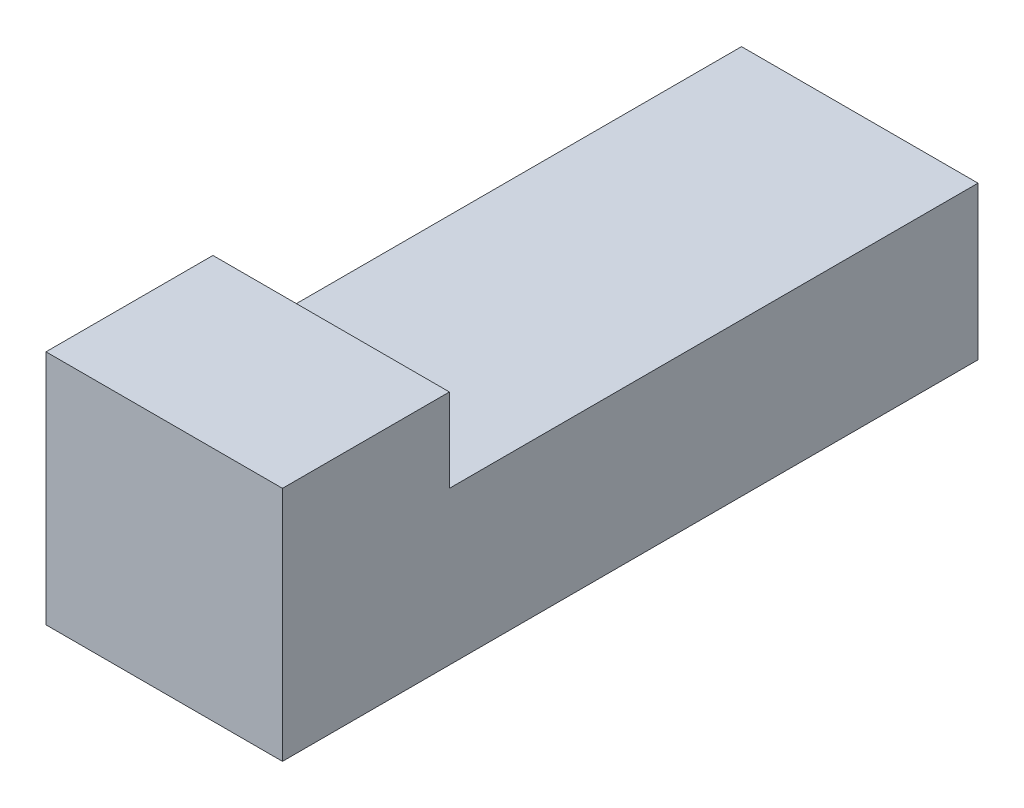
SolidWorks part; units mm, degrees
ref_plane "Front Plane" through (0, 0, 0) normal (0, 0, 1) x (1, 0, 0)
ref_plane "Top Plane" through (0, 0, 0) normal (0, 1, 0) x (1, 0, 0)
ref_plane "Right Plane" through (0, 0, 0) normal (1, 0, 0) x (0, 0, -1)
sketch "Sketch1" plane through (0, 0, 0) normal (0, 0, 1) x (1, 0, 0)
  line L1 (-34.281, 1.383) -> (-29.963, 1.383)
  line L2 (-34.281, 1.383) -> (-34.281, -2.935)
  line L3 (-34.281, -2.935) -> (-29.963, -2.935)
  line L4 (-29.963, 1.383) -> (-29.963, -2.935)
extrude "Boss-Extrude1" add sketch "Sketch1" along normal blind 12.7
ref_plane "Plane1" through (0, 0, 9.652) normal (0, 0, 1) x (1, 0, 0)
sketch "Sketch2" plane through (0, 0, 9.652) normal (0, 0, 1) x (1, 0, 0)
  line L0 (-29.963, -2.935) -> (-29.963, 1.383) construction
  line L1 (-34.281, 1.383) -> (-29.963, 1.383)
  line L2 (-34.281, 1.383) -> (-34.281, -0.141)
  line L3 (-34.281, -0.141) -> (-29.963, -0.141)
  line L4 (-29.963, 1.383) -> (-29.963, -0.141)
extrude "Cut-Extrude1" cut sketch "Sketch2" against normal blind 12.7
